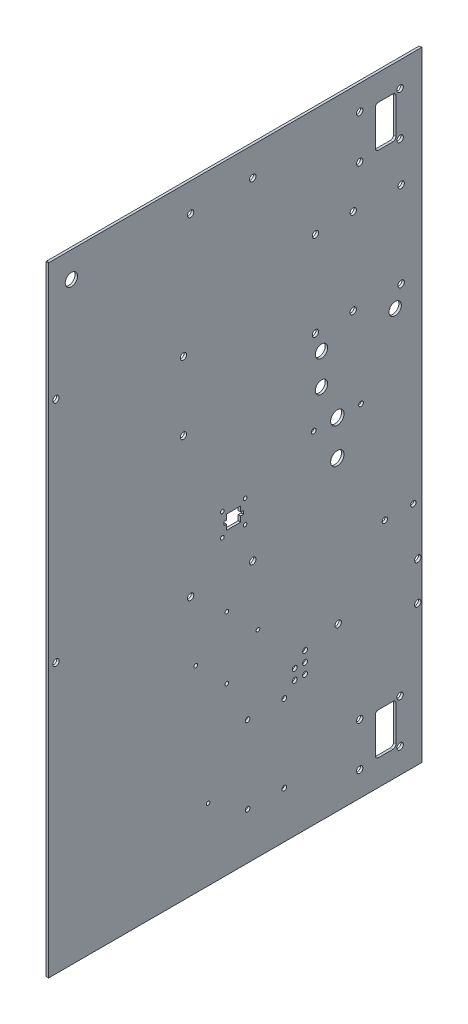
SolidWorks part; units mm, degrees
material "Acrylic (Medium-high impact)"
ref_plane "Front Plane" through (0, 0, 0) normal (0, 0, 1) x (1, 0, 0)
ref_plane "Top Plane" through (0, 0, 0) normal (0, 1, 0) x (1, 0, 0)
ref_plane "Right Plane" through (0, 0, 0) normal (1, 0, 0) x (0, 0, -1)
sketch "Sketch1" plane through (0, 0, 0) normal (1, 0, 0) x (0, 0, -1)
  line L0 (-249.6566, 398.5133) -> (-249.6566, 401.5867) construction
  line L1 (249.6566, -398.5133) -> (-249.6566, -398.5133)
  line L2 (249.6566, -398.5133) -> (249.6566, 398.5133)
  line L3 (249.6566, 398.5133) -> (-249.6566, 398.5133)
  line L4 (-249.6566, -398.5133) -> (-249.6566, 398.5133)
  line L5 (249.6566, -398.5133) -> (-249.6566, 398.5133) construction
  line L6 (249.6566, 398.5133) -> (-249.6566, -398.5133) construction
  line L7 (-249.6566, -398.5133) -> (-249.6566, -411.2133) construction
  line L8 (-249.6566, 398.5133) -> (-252.73, 398.5133) construction
  point P0 (0, 0)
  dimension "D2" = 3.0734
  dimension "D3" = 12.7
  dimension "D4" = 812.8
  dimension "D5" = 3.0734
  dimension "D1" = 502.3866
extrude "SidePanel" add sketch "Sketch1" along normal blind 3.0734
sketch "Sketch2" plane through (3.0734, 0, 0) normal (1, 0, 0) x (0, 0, -1)
  line L0 (192.5066, 398.5133) -> (192.5066, 379.4633) construction
  line L1 (249.6566, 398.5133) -> (-249.6566, 398.5133) construction
  line L2 (249.6566, -398.5133) -> (249.6566, 398.5133) construction
  line L3 (192.5066, -398.5133) -> (192.5066, -379.4633) construction
  line L4 (-249.6566, -398.5133) -> (249.6566, -398.5133) construction
  line L7 (249.6566, 338.1883) -> (230.6066, 338.1883) construction
  circle A0 centre (192.5066, 388.9883) radius 2.8956
  circle A1 centre (192.5066, -388.9883) radius 2.8956
  dimension "D3" = 5.7912
  dimension "D1" = 19.05
  dimension "D4" = 19.05
  dimension "D6" = 19.05
  dimension "D2" = 38.1
extrude "TopBottomHoleMaster" cut sketch "Sketch2" against normal through all
pattern_linear "LPattern1" count 4 spacing 127.0677 along (0, 0, 1) of "TopBottomHoleMaster"
sketch "Sketch3" plane through (3.0734, 0, 0) normal (1, 0, 0) x (0, 0, -1)
  line L1 (249.6566, -398.5133) -> (249.6566, 398.5133) construction
  line L2 (249.6566, 315.8617) -> (230.6066, 315.8617) construction
  line L3 (249.6566, 398.5133) -> (249.6566, 401.5867) construction
  line L4 (249.6566, 398.5133) -> (-249.6566, 398.5133) construction
  line L8 (-245.8466, 315.8617) -> (-226.7966, 315.8617) construction
  line L10 (249.6566, -398.5133) -> (249.6566, 398.5133) construction
  circle A0 centre (-236.3216, 315.8617) radius 2.8956
  circle A1 centre (240.1316, 315.8617) radius 2.8956
  dimension "D5" = 5.7912
  dimension "D2" = 19.05
  dimension "D3" = 3.0734
  dimension "D4" = 85.725
  dimension "D1" = 457.4032
extrude "RearHolesMaster" cut sketch "Sketch3" against normal through all
pattern_linear "LPattern2" count 4 spacing 211.7344 along (0, -1, 0) of "RearHolesMaster"
sketch "Sketch4" plane through (0, 0, 0) normal (-1, 0, 0) x (0, 0, 1)
  line L0 (-249.6566, -398.5133) -> (-249.6566, 398.5133) construction
  line L1 (-249.6566, 398.5133) -> (-230.6066, 398.5133)
  line L2 (-249.6566, 398.5133) -> (-249.6566, 379.4633)
  line L3 (-249.6566, 379.4633) -> (-230.6066, 379.4633)
  line L4 (-230.6066, 398.5133) -> (-230.6066, 379.4633)
  line L5 (249.6566, 398.5133) -> (226.7966, 398.5133)
  line L6 (249.6566, 398.5133) -> (249.6566, 379.4633)
  line L7 (249.6566, 379.4633) -> (226.7966, 379.4633)
  line L8 (226.7966, 398.5133) -> (226.7966, 379.4633)
  line L9 (-249.6566, -398.5133) -> (-230.6066, -398.5133)
  line L10 (-249.6566, -398.5133) -> (-249.6566, -379.4633)
  line L11 (-249.6566, -379.4633) -> (-230.6066, -379.4633)
  line L12 (-230.6066, -398.5133) -> (-230.6066, -379.4633)
  line L13 (249.6566, -398.5133) -> (-249.6566, -398.5133) construction
  line L14 (236.3216, 315.8617) -> (236.3216, 379.4633) construction
  dimension "D1" = 19.05
  dimension "D2" = 9.525
extrude "CornerCuts" cut sketch "Sketch4" against normal through all
hole_wizard "#8 Clearance Hole4 Brain Mount" positions "Sketch13" profile "Sketch14" hole size "5/16" standard "ANSI Inch" end condition through all
sketch "Sketch13" plane through (0, 0, 0) normal (-1, 0, 0) x (0, 0, 1)
  line L1 (-23.3934, 344.4367) -> (52.8066, 344.4367) construction
  line L2 (-23.3934, 344.4367) -> (-23.3934, -61.9633) construction
  line L3 (-23.3934, -61.9633) -> (52.8066, -61.9633) construction
  line L4 (52.8066, 344.4367) -> (52.8066, -61.9633) construction
  line L6 (249.6566, 379.4633) -> (249.6566, -398.5133) construction
  line L7 (-230.6066, 398.5133) -> (226.7966, 398.5133) construction
  point P0 (-23.3934, 344.4367)
  point P2 (52.8066, 344.4367)
  point P4 (52.8066, -61.9633)
  point P6 (-23.3934, -61.9633)
  point P78 (-146.4564, 141.8717)
  point P80 (-146.4564, 247.2817)
  point P81 (61.5696, 197.4926)
  point P83 (61.5696, 113.4186)
  dimension "D3" = 196.85
  dimension "D4" = 54.0766
  dimension "D1" = 76.2
  dimension "D2" = 406.4
  dimension "D5" = 123.063
  dimension "D6" = 203.835
  dimension "D7" = 105.41
  dimension "D8" = 84.074
  dimension "D9" = 8.763
  dimension "D10" = 175.3819
sketch "Sketch14" plane through (0, 344.4367, -23.3934) normal (0, 1, 0) x (0, 0, 1)
  line L0 (0, 0) -> (0, 3.0734)
  line L1 (0, 3.0734) -> (3.9116, 3.0734)
  line L2 (3.9116, 3.0734) -> (3.9116, 0)
  line L5 (3.9116, 0) -> (0, 0)
  line L11 (0, -6.35) -> (0, 107.95) construction
  dimension "Thru Hole Dia." = 7.8232
  dimension "Thru Hole Depth" = 3.0734
hole_wizard "#8 Clearance Hole3 Pump Mounts" positions "Sketch15" profile "Sketch16" hole size "#8" standard "ANSI Inch" end condition through all
sketch "Sketch15" plane through (0, 0, 0) normal (-1, 0, 0) x (0, 0, 1)
  line L4 (8.3566, -100.0633) -> (8.3566, -176.2633) construction
  line L5 (8.3566, -100.0633) -> (8.3566, -61.9633) construction
  line L7 (8.3566, -138.1633) -> (46.4566, -138.1633) construction
  line L9 (8.3566, -138.1633) -> (-29.7434, -138.1633) construction
  line L10 (-23.3934, -61.9633) -> (52.8066, -61.9633) construction
  point P0 (46.4566, -138.1633)
  point P2 (8.3566, -100.0633)
  point P4 (8.3566, -176.2633)
  point P6 (-29.7434, -138.1633)
  dimension "D1" = 76.2
  dimension "D2" = 76.2
  dimension "D3" = 38.1
  dimension "D4" = 44.45
sketch "Sketch16" plane through (0, -138.1633, 46.4566) normal (0, 1, 0) x (0, 0, 1)
  line L0 (0, 0) -> (0, 3.0734)
  line L1 (0, 3.0734) -> (2.2479, 3.0734)
  line L2 (2.2479, 3.0734) -> (2.2479, 0)
  line L5 (2.2479, 0) -> (0, 0)
  line L11 (0, -6.35) -> (0, 107.95) construction
  dimension "Thru Hole Dia." = 4.4958
  dimension "Thru Hole Depth" = 3.0734
sketch "Sketch17" plane through (0, 0, 0) normal (-1, 0, 0) x (0, 0, 1)
  line L3 (-230.6066, 379.4633) -> (226.7966, 379.4633) construction
  line L4 (-230.6066, 379.4633) -> (-230.6066, -379.4633) construction
  line L5 (-230.6066, -379.4633) -> (249.6566, -379.4633) construction
  line L6 (-198.8566, 347.7133) -> (-173.4566, 347.7133)
  line L7 (-198.8566, 347.7133) -> (-198.8566, 296.9133)
  line L8 (-198.8566, 296.9133) -> (-173.4566, 296.9133)
  line L9 (-173.4566, 347.7133) -> (-173.4566, 296.9133)
  line L10 (-173.4566, -347.7133) -> (-173.4566, -296.9133)
  line L11 (-173.4566, -347.7133) -> (-198.8566, -347.7133)
  line L12 (-198.8566, -347.7133) -> (-198.8566, -296.9133)
  line L13 (-173.4566, -296.9133) -> (-198.8566, -296.9133)
  line L14 (249.6566, 379.4633) -> (249.6566, -398.5133) construction
  dimension "D1" = 25.4
  dimension "D4" = 50.8
  dimension "D2" = 50.8
  dimension "D3" = 25.4
  dimension "D5" = 31.75
  dimension "D6" = 31.75
  dimension "D7" = 31.75
extrude "Cable Pass Through" cut sketch "Sketch17" against normal through all
hole_wizard "#8 Clearance Hole1 Pass through Mounting holes" positions "Sketch48" profile "Sketch49" hole size "5/16" standard "ANSI Inch" end condition through all
sketch "Sketch48" plane through (3.0734, 0, 0) normal (1, 0, 0) x (0, 0, -1)
  line L21 (154.4066, 348.9833) -> (154.4066, 295.6433) construction
  line L24 (203.9366, 348.9833) -> (203.9366, 295.6433) construction
  line L27 (203.9366, 322.3133) -> (154.4066, 322.3133) construction
  line L30 (173.4566, 322.3133) -> (198.8566, 322.3133) construction
  line L31 (173.4566, 296.9133) -> (173.4566, 347.7133) construction
  line L32 (198.8566, 347.7133) -> (198.8566, 296.9133) construction
  line L34 (173.4566, 296.9133) -> (173.4566, 347.7133) construction
  line L36 (154.4066, -295.6433) -> (154.4066, -348.9833) construction
  line L37 (154.4066, -322.3133) -> (173.4566, -322.3133) construction
  line L38 (173.4566, -347.7133) -> (173.4566, -296.9133) construction
  line L41 (203.9366, -295.6433) -> (203.9366, -348.9833) construction
  line L44 (198.8566, -322.3133) -> (203.9366, -322.3133) construction
  line L45 (198.8566, -296.9133) -> (198.8566, -347.7133) construction
  point P0 (154.4066, -348.9833)
  point P2 (203.9366, -348.9833)
  point P4 (203.9366, -295.6433)
  point P6 (154.4066, -295.6433)
  point P63 (154.4066, 348.9833)
  point P65 (203.9366, 348.9833)
  point P67 (203.9366, 295.6433)
  point P69 (154.4066, 295.6433)
  dimension "D1" = 5.08
  dimension "D2" = 19.05
  dimension "D3" = 53.34
  dimension "D4" = 5.08
  dimension "D5" = 19.05
  dimension "D6" = 53.34
sketch "Sketch49" plane through (3.0734, -348.9833, -154.4066) normal (0, 1, 0) x (0, 0, -1)
  line L0 (0, 0) -> (0, 3.0734)
  line L1 (0, 3.0734) -> (3.9116, 3.0734)
  line L2 (3.9116, 3.0734) -> (3.9116, 0)
  line L5 (3.9116, 0) -> (0, 0)
  line L11 (0, -6.35) -> (0, 107.95) construction
  dimension "Thru Hole Dia." = 7.8232
  dimension "Thru Hole Depth" = 3.0734
hole_wizard "#8 Clearance Hole3 Sensor Mounts" positions "Sketch25" profile "Sketch24" hole size "#8" standard "ANSI Inch"
sketch "Sketch25" plane through (0, 0, 0) normal (-1, 0, 0) x (0, 0, 1)
  line L3 (-21.0566, -36.5633) -> (55.1434, -36.5633) construction
  line L4 (-21.0566, -36.5633) -> (-21.0566, 39.6367) construction
  line L5 (-21.0566, 39.6367) -> (55.1434, 39.6367) construction
  line L6 (55.1434, -36.5633) -> (55.1434, 39.6367) construction
  line L8 (-21.0566, 39.6367) -> (55.1434, 39.6367) construction
  line L9 (-21.0566, 39.6367) -> (-21.0566, 77.7367) construction
  line L10 (-21.0566, 77.7367) -> (55.1434, 77.7367) construction
  line L11 (55.1434, 39.6367) -> (55.1434, 77.7367) construction
  point P38 (55.1434, 39.6367)
  point P135 (-21.0566, 39.6367)
  point P146 (55.1434, 77.7367)
  point P235 (-21.0566, 77.7367)
  dimension "D1" = 76.2
  dimension "D2" = 76.2
  dimension "D3" = 38.1
  dimension "D4" = 76.2
sketch "Sketch24" plane through (0, 39.6367, 55.1434) normal (0, 1, 0) x (0, 0, 1)
  line L0 (0, 0) -> (0, 3.0734)
  line L1 (0, 3.0734) -> (2.2479, 3.0734)
  line L2 (2.2479, 3.0734) -> (2.2479, 0)
  line L5 (2.2479, 0) -> (0, 0)
  line L11 (0, -6.35) -> (0, 107.95) construction
  dimension "Thru Hole Dia." = 4.4958
  dimension "Thru Hole Depth" = 3.0734
sketch "Sketch39" plane through (0, 0, 0) normal (-1, 0, 0) x (0, 0, 1)
  line L0 (-249.6566, 398.5133) -> (-249.6566, 418.9221) construction
  line L1 (-230.2256, 398.5133) -> (-230.6066, 398.5133)
  line L2 (-249.6566, -398.5133) -> (-249.6566, -414.8093) construction
  line L3 (-230.6066, 398.5133) -> (-230.6066, 379.4633)
  line L4 (-230.6066, 379.4633) -> (-249.6566, 379.4633)
  line L5 (-249.6566, 379.0823) -> (-230.2256, 379.0823)
  line L6 (-230.2256, 398.5133) -> (-230.2256, 379.0823)
  line L7 (-249.6566, -398.5133) -> (-270.6931, -398.5133) construction
  line L8 (-249.6566, -379.0823) -> (-249.6566, -379.4633)
  line L9 (-249.6566, -379.4633) -> (-230.6066, -379.4633)
  line L10 (-230.6066, -379.4633) -> (-230.6066, -398.5133)
  line L11 (-249.6566, -379.0823) -> (-230.2256, -379.0823)
  line L12 (-230.2256, -398.5133) -> (-230.2256, -379.0823)
  line L13 (-230.6066, -398.5133) -> (-230.2256, -398.5133)
  line L14 (-249.6566, 379.4633) -> (-249.6566, 379.0823)
  line L15 (226.7966, 398.5133) -> (226.4156, 398.5133)
  line L16 (-230.6066, 398.5133) -> (226.7966, 398.5133) construction
  line L17 (226.4156, 398.5133) -> (226.4156, 379.0823)
  line L18 (249.6566, 379.0823) -> (226.4156, 379.0823)
  line L19 (249.6566, 379.4633) -> (249.6566, -398.5133) construction
  line L20 (226.7966, 398.5133) -> (226.7966, 379.4633)
  line L21 (226.7966, 379.4633) -> (249.6566, 379.4633)
  line L22 (249.6566, 379.4633) -> (249.6566, 379.0823)
  dimension "D1" = 19.431
  dimension "D2" = 19.431
  dimension "D3" = 19.431
  dimension "D4" = 19.431
  dimension "D5" = 0.381
extrude "Cut-Extrude1" cut sketch "Sketch39" against normal blind 2.54
hole_wizard "#8 Clearance Hole -hx mount" positions "Sketch40" profile "Sketch41" hole size "5/16" standard "ANSI Inch" end condition through all
sketch "Sketch40" plane through (3.0734, 0, 0) normal (1, 0, 0) x (0, 0, -1)
  line L0 (230.6066, 398.5133) -> (-226.7966, 398.5133) construction
  line L1 (249.6566, -379.4633) -> (249.6566, 379.4633) construction
  point P0 (205.2066, 246.1133)
  point P2 (205.2066, 141.1133)
  point P4 (100.2066, 141.1133)
  point P6 (100.2066, 246.1133)
  dimension "D1" = 152.4
  dimension "D2" = 44.45
  dimension "D3" = 105
  dimension "D4" = 105
sketch "Sketch41" plane through (3.0734, 246.1133, -205.2066) normal (0, 1, 0) x (0, 0, -1)
  line L0 (0, 0) -> (0, 3.0734)
  line L1 (0, 3.0734) -> (3.9116, 3.0734)
  line L2 (3.9116, 3.0734) -> (3.9116, 0)
  line L5 (3.9116, 0) -> (0, 0)
  line L11 (0, -6.35) -> (0, 107.95) construction
  dimension "Thru Hole Dia." = 7.8232
  dimension "Thru Hole Depth" = 3.0734
sketch "Sketch42" plane through (3.0734, 0, 0) normal (1, 0, 0) x (0, 0, -1)
  line L0 (100.2066, 141.1133) -> (205.2066, 141.1133) construction
  line L1 (107.5726, 118.5073) -> (197.8406, 118.5073) construction
  line L2 (152.7066, 141.1133) -> (152.7066, 118.5073) construction
  circle A0 centre (197.8406, 118.5073) radius 7.5787
  circle A1 centre (107.5726, 118.5073) radius 7.5819
  circle A2 centre (197.8406, 118.5073) radius 21.6881 construction
  dimension "D1" = 15.1574
  dimension "D2" = 15.1638
  dimension "D4" = 22.606
  dimension "D3" = 7.366
extrude "Coolant hose pass through" cut sketch "Sketch42" against normal through all
sketch "Sketch43" plane through (3.0734, 0, 0) normal (1, 0, 0) x (0, 0, -1)
  line L0 (-249.6566, 379.4633) -> (-249.6566, -398.5133) construction
  line L1 (230.6066, 398.5133) -> (-226.7966, 398.5133) construction
  line L2 (107.5726, 118.5073) -> (197.8406, 118.5073) construction
  line L3 (107.5726, 118.5073) -> (107.5726, 80.4073) construction
  circle A0 centre (-198.8566, 347.7133) radius 7.5819
  circle A1 centre (107.5726, 80.4073) radius 7.5819
  dimension "D1" = 15.1638
  dimension "D4" = 15.1638
  dimension "D5" = 38.1
  dimension "D2" = 50.8
  dimension "D3" = 50.8
extrude "Air flush in/out" cut sketch "Sketch43" against normal through all
hole_wizard "#8 Clearance Hole2 Air Flush Out mount" positions "Sketch44" profile "Sketch45" hole size "5/16" standard "ANSI Inch" end condition through all
sketch "Sketch44" plane through (3.0734, 0, 0) normal (1, 0, 0) x (0, 0, -1)
  line L0 (249.6566, -379.4633) -> (249.6566, 379.4633) construction
  line L1 (-249.6566, -398.5133) -> (230.6066, -398.5133) construction
  point P0 (225.5266, -160.7693)
  point P2 (225.5266, -208.0133)
  point P4 (128.0678, -181.1548)
  dimension "D1" = 47.244
  dimension "D2" = 99.568
  dimension "D3" = 101.092
  dimension "D4" = 24.13
  dimension "D5" = 190.5
sketch "Sketch45" plane through (3.0734, -160.7693, -225.5266) normal (0, 1, 0) x (0, 0, -1)
  line L0 (0, 0) -> (0, 3.0734)
  line L1 (0, 3.0734) -> (3.9116, 3.0734)
  line L2 (3.9116, 3.0734) -> (3.9116, 0)
  line L5 (3.9116, 0) -> (0, 0)
  line L11 (0, -6.35) -> (0, 107.95) construction
  dimension "Thru Hole Dia." = 7.8232
  dimension "Thru Hole Depth" = 3.0734
hole_wizard "#8 Clearance Hole4 Panel Mounts" positions "Sketch46" profile "Sketch47" hole size "5/16" standard "ANSI Inch" end condition through all
sketch "Sketch46" plane through (3.0734, 0, 0) normal (1, 0, 0) x (0, 0, -1)
  line L0 (-249.6566, 379.4633) -> (-249.6566, -398.5133) construction
  line L1 (230.6066, 398.5133) -> (-226.7966, 398.5133) construction
  point P0 (-217.7034, 230.1367)
  point P6 (-217.7034, -49.2633)
  dimension "D1" = 31.9532
  dimension "D2" = 168.3766
  dimension "D3" = 279.4
sketch "Sketch47" plane through (3.0734, 230.1367, 217.7034) normal (0, 1, 0) x (0, 0, -1)
  line L0 (0, 0) -> (0, 3.0734)
  line L1 (0, 3.0734) -> (3.9116, 3.0734)
  line L2 (3.9116, 3.0734) -> (3.9116, 0)
  line L5 (3.9116, 0) -> (0, 0)
  line L11 (0, -6.35) -> (0, 107.95) construction
  dimension "Thru Hole Dia." = 7.8232
  dimension "Thru Hole Depth" = 3.0734
fillet "Fillet1" radius 3.81 8 edges at (1.5367, -296.9133, -173.4566) (1.5367, -296.9133, -198.8566) (1.5367, -347.7133, -198.8566) (1.5367, -347.7133, -173.4566) (1.5367, 347.7133, -198.8566) (1.5367, 347.7133, -173.4566) (1.5367, 296.9133, -198.8566) (1.5367, 296.9133, -173.4566)
sketch "Sketch50" plane through (3.0734, 0, 0) normal (1, 0, 0) x (0, 0, -1)
  line L0 (-8.625, 3.8117) -> (8.625, 3.8117)
  line L1 (8.625, 3.8117) -> (8.625, -2.6883)
  line L2 (8.625, -2.6883) -> (12.125, -2.6883)
  line L3 (12.125, -2.6883) -> (12.125, -6.9383)
  line L4 (12.125, -6.9383) -> (8.625, -6.9383)
  line L5 (8.625, -6.9383) -> (8.625, -13.4383)
  line L6 (8.625, -13.4383) -> (-8.625, -13.4383)
  line L7 (-8.625, -13.4383) -> (-8.625, -6.9383)
  line L8 (-8.625, -6.9383) -> (-12.125, -6.9383)
  line L9 (-12.125, -6.9383) -> (-12.125, -2.6883)
  line L10 (-12.125, -2.6883) -> (-8.625, -2.6883)
  line L11 (-8.625, -2.6883) -> (-8.625, 3.8117)
  line L12 (127, -4.8133) -> (127, 38.3667) construction
  line L17 (0, 3.8117) -> (0, -13.4383) construction
  line L18 (-12.125, -4.8133) -> (12.125, -4.8133) construction
  line L19 (-3.4982, 3.8117) -> (-3.4982, -13.4383) construction
  line L20 (127, -4.8133) -> (0, -4.8133) construction
  line L21 (13.97, 9.1567) -> (13.97, -18.7833) construction
  line L22 (-249.6566, -9.525) -> (249.6566, -9.525) construction
  line L23 (98, 38.3667) -> (156, 38.3667) construction
  line L24 (-19.05, 14.2367) -> (19.05, 14.2367) construction
  line L25 (19.05, 14.2367) -> (19.05, -23.8633) construction
  line L26 (-13.97, -18.7833) -> (13.97, -18.7833) construction
  line L27 (-19.05, -23.8633) -> (-19.05, 14.2367) construction
  line L28 (-19.05, -4.8133) -> (19.05, -4.8133) construction
  line L29 (0, 14.2367) -> (0, -23.8633) construction
  line L30 (0, -13.4383) -> (0, -18.7833) construction
  line L31 (-249.6566, -398.5133) -> (230.6066, -398.5133) construction
  line L32 (0, 398.5133) -> (0, -398.5133) construction
  line L41 (230.6066, -379.4633) -> (249.6566, -379.4633)
  line L42 (249.6566, -379.4633) -> (249.6566, 379.4633)
  line L43 (249.6566, 379.4633) -> (230.6066, 379.4633)
  line L44 (230.6066, 379.4633) -> (230.6066, 398.5133)
  line L45 (230.6066, 398.5133) -> (-226.7966, 398.5133)
  line L46 (-226.7966, 398.5133) -> (-226.7966, 379.4633)
  line L47 (-226.7966, 379.4633) -> (-249.6566, 379.4633)
  line L48 (-249.6566, 379.4633) -> (-249.6566, -398.5133)
  line L49 (-249.6566, -398.5133) -> (230.6066, -398.5133)
  line L50 (230.6066, -398.5133) -> (230.6066, -379.4633)
  line L51 (230.6066, -379.4633) -> (249.6566, -379.4633)
  line L52 (249.6566, -379.4633) -> (249.6566, 379.4633)
  line L53 (249.6566, 379.4633) -> (230.6066, 379.4633)
  line L54 (230.6066, 379.4633) -> (230.6066, 398.5133)
  line L55 (230.6066, 398.5133) -> (-226.7966, 398.5133)
  line L56 (-226.7966, 398.5133) -> (-226.7966, 379.4633)
  line L57 (-226.7966, 379.4633) -> (-249.6566, 379.4633)
  line L58 (-249.6566, 379.4633) -> (-249.6566, -398.5133)
  line L59 (-249.6566, -398.5133) -> (230.6066, -398.5133)
  line L60 (230.6066, -398.5133) -> (230.6066, -379.4633)
  circle A0 centre (127, -4.8133) radius 8.1915
  circle A1 centre (127, 38.3667) radius 8.1915
  point P17 (0, 3.8117)
  point P26 (0, -4.8133)
  point P27 (-3.4982, -4.8133)
  point P28 (-13.97, -18.7833)
  point P31 (13.97, -18.7833)
  point P34 (98, 38.3667)
  point P35 (156, 38.3667)
  point P38 (127, 38.3667)
  point P47 (0, -4.8133)
  point P48 (-13.97, 9.1567)
  point P49 (13.97, 9.1567)
  point P52 (13.97, -4.8133)
  point P67 (0, -9.525)
  dimension "D2" = 16.383
  dimension "D19" = 16.383
  dimension "D3" = 17.25
  dimension "D4" = 17.25
  dimension "D7" = 4.25
  dimension "D8" = 24.25
  dimension "D9" = 127
  dimension "D10" = 393.7
  dimension "D12" = 43.18
  dimension "D13" = 58
  dimension "D14" = 38.1
  dimension "D15" = 38.1
  dimension "D16" = 27.94
  dimension "D17" = 27.94
  dimension "D18" = 0
extrude "Sensor Mounting" cut sketch "Sketch50" against normal through all flip side to cut
hole_wizard "#8 Clearance Hole1" positions "Sketch51" profile "Sketch52" hole size "#8" standard "ANSI Inch" end condition through all
sketch "Sketch51" plane through (3.0734, 0, 0) normal (1, 0, 0) x (0, 0, -1)
  point P0 (-13.97, 9.1567)
  point P3 (13.97, 9.1567)
  point P6 (13.97, -18.7833)
  point P9 (-13.97, -18.7833)
sketch "Sketch52" plane through (3.0734, 9.1567, 13.97) normal (0, 1, 0) x (0, 0, -1)
  line L0 (0, 0) -> (0, 3.0734)
  line L1 (0, 3.0734) -> (2.2479, 3.0734)
  line L2 (2.2479, 3.0734) -> (2.2479, 0)
  line L5 (2.2479, 0) -> (0, 0)
  line L11 (0, -6.35) -> (0, 107.95) construction
  dimension "Thru Hole Dia." = 4.4958
  dimension "Thru Hole Depth" = 3.0734
hole_wizard "#12 Clearance Hole1" positions "Sketch53" profile "Sketch54" hole size "#12" standard "ANSI Inch" end condition through all
sketch "Sketch53" plane through (3.0734, 0, 0) normal (1, 0, 0) x (0, 0, -1)
  point P0 (98, 38.3667)
  point P3 (156, 38.3667)
sketch "Sketch54" plane through (3.0734, 38.3667, -98) normal (0, 1, 0) x (0, 0, -1)
  line L0 (0, 0) -> (0, 3.0734)
  line L1 (0, 3.0734) -> (2.8956, 3.0734)
  line L2 (2.8956, 3.0734) -> (2.8956, 0)
  line L5 (2.8956, 0) -> (0, 0)
  line L11 (0, -6.35) -> (0, 107.95) construction
  dimension "Thru Hole Dia." = 5.7912
  dimension "Thru Hole Depth" = 3.0734
fillet "Fillet2" radius 0.127 12 edges at (1.5367, -13.4383, 8.625) (1.5367, -6.9383, -12.125) (1.5367, -13.4383, -8.625) (1.5367, -6.9383, -8.625) (1.5367, -2.6883, -12.125) (1.5367, -2.6883, -8.625) (1.5367, -6.9383, 8.625) (1.5367, -2.6883, 8.625) (1.5367, -2.6883, 12.125) (1.5367, -6.9383, 12.125) (1.5367, 3.8117, -8.625) (1.5367, 3.8117, 8.625)
hole_wizard "#4 Clearance Hole compressor driver" positions "Sketch55" profile "Sketch56" hole size "#12" standard "ANSI Inch" end condition through all
sketch "Sketch55" plane through (0, 0, 0) normal (-1, 0, 0) x (0, 0, 1)
  line L0 (249.6566, -398.5133) -> (-230.2256, -398.5133) construction
  line L2 (249.6566, 379.0823) -> (249.6566, -398.5133) construction
  point P0 (-17.0434, -227.3133)
  point P2 (-62.0434, -227.3133)
  point P4 (-62.0434, -322.3133)
  point P6 (-17.0434, -322.3133)
  dimension "D1" = 45
  dimension "D2" = 95
  dimension "D3" = 76.2
  dimension "D4" = 266.7
sketch "Sketch56" plane through (0, -227.3133, -17.0434) normal (0, 1, 0) x (0, 0, 1)
  line L0 (0, 0) -> (0, 3.0734)
  line L1 (0, 3.0734) -> (2.8956, 3.0734)
  line L2 (2.8956, 3.0734) -> (2.8956, 0)
  line L5 (2.8956, 0) -> (0, 0)
  line L11 (0, -6.35) -> (0, 107.95) construction
  dimension "Thru Hole Dia." = 5.7912
  dimension "Thru Hole Depth" = 3.0734
hole_wizard "1/4 Clearance Hole ball valve u bolt" positions "Sketch57" profile "Sketch58" hole size "1/4" standard "ANSI Inch" end condition through all
sketch "Sketch57" plane through (3.0734, 0, 0) normal (1, 0, 0) x (0, 0, -1)
  line L0 (-249.6566, -398.5133) -> (230.6066, -398.5133) construction
  line L1 (249.6566, -379.4633) -> (249.6566, 379.4633) construction
  point P0 (220.1418, -99.7331)
  point P2 (185.2168, -99.7331)
  dimension "D1" = 298.7802
  dimension "D2" = 29.5148
  dimension "D3" = 34.925
sketch "Sketch58" plane through (3.0734, -99.7331, -220.1418) normal (0, 1, 0) x (0, 0, -1)
  line L0 (0, 0) -> (0, 3.0734)
  line L1 (0, 3.0734) -> (3.2639, 3.0734)
  line L2 (3.2639, 3.0734) -> (3.2639, 0)
  line L5 (3.2639, 0) -> (0, 0)
  line L11 (0, -6.35) -> (0, 107.95) construction
  dimension "Thru Hole Dia." = 6.5278
  dimension "Thru Hole Depth" = 3.0734
hole_wizard "Aeration Pump #8 Clearance Hole1" positions "Sketch59" profile "Sketch60" hole size "#8" standard "ANSI Inch" end condition through all
sketch "Sketch59" plane through (3.0734, 0, 0) normal (1, 0, 0) x (0, 0, -1)
  line L0 (-36.1378, -296.9133) -> (-5.1816, -296.9133) construction
  line L1 (-5.1816, -296.9133) -> (-5.1816, -286.5946) construction
  line L2 (-5.1816, -286.5946) -> (-36.1378, -286.5946) construction
  line L3 (-36.1378, -286.5946) -> (-36.1378, -296.9133) construction
  line L6 (-36.1378, -291.7539) -> (-5.1816, -291.7539) construction
  line L9 (-31.3753, -286.5946) -> (-31.3753, -296.9133) construction
  circle A0 centre (17.0434, -322.3133) radius 2.8956 construction
  point P0 (-31.3753, -291.7539)
  dimension "D4" = 22.225
  dimension "D5" = 25.4
  dimension "D1" = 10.3187
  dimension "D2" = 30.9562
  dimension "D3" = 4.7625
sketch "Sketch60" plane through (3.0734, -291.7539, 31.3753) normal (0, 1, 0) x (0, 0, -1)
  line L0 (0, 0) -> (0, 3.0734)
  line L1 (0, 3.0734) -> (2.1526, 3.0734)
  line L2 (2.1526, 3.0734) -> (2.1527, 0)
  line L5 (2.1527, 0) -> (0, 0)
  line L11 (0, -6.35) -> (0, 107.95) construction
  dimension "Thru Hole Dia." = 4.3053
  dimension "Thru Hole Depth" = 3.0734
sketch "Nutrient Holes" plane through (3.0734, 0, 0) normal (1, 0, 0) x (0, 0, -1)
  line L0 (-249.6566, -398.5133) -> (230.6066, -398.5133) construction
  circle A0 centre (87.4434, -214.3633) radius 3.0226
  circle A1 centre (62.0434, -227.3133) radius 2.8956 construction
  dimension "D1" = 6.0452
  dimension "D2" = 184.15
  dimension "D3" = 25.4
extrude "Nutrient Hoses" cut sketch "Nutrient Holes" against normal through all
pattern_linear "LPattern3" count 3 spacing 12.7 along (0, 1, 0) count 3 spacing 12.7 along (0, 0, 1) skipping (0, 2), (1, 2), (2, 1), (2, 2) of "Nutrient Hoses"
sketch "Sketch61" plane through (3.0734, 0, 0) normal (1, 0, 0) x (0, 0, -1)
  line L0 (-226.7966, 379.4633) -> (230.6066, 379.4633)
  line L1 (230.6066, 379.4633) -> (230.6066, -379.4633)
  line L2 (-226.7966, 379.4633) -> (-226.7966, -379.4633)
  line L3 (-226.7966, -379.4633) -> (230.6066, -379.4633)
  line L4 (-252.1966, 404.8633) -> (-252.1966, -404.8633)
  line L5 (-252.1966, -404.8633) -> (256.0066, -404.8633)
  line L6 (256.0066, 404.8633) -> (256.0066, -404.8633)
  line L7 (-252.1966, 404.8633) -> (256.0066, 404.8633)
  dimension "D1" = 25.4
extrude "Cut-Extrude2" cut sketch "Sketch61" against normal through all
equation "\"Height\"= 32in"
equation "\"Width\"= 23in"
equation "\"Depth\"= 20in"
equation "\"Plexi\"= .121in"
equation "\"Cutwidth\"= .016in"
equation "\"Earsize\"= 1in + \"Cutwidth\" /2"
equation "\"Slotsize\" = 1in - \"CutWidth\" / 2"
equation "\"InnerWidth\" = \"Width\" - 2* \"Plexi\""
equation "\"InnerHeight\" = \"Height\" -2 * \"Plexi\""
equation "\"InnerDepth\" = \"Depth\" - 2*\"Plexi\""
equation "\"RearHoleSpacing\" = (\"Width\" - 2*\"RearHolesBorder\") / (\"RearNumHoles\"-1)"
equation "\"RivetDia\" = .228in"
equation "\"SlotDepth\" = \"Plexi\" + 0.75in + .005in"
equation "\"SideSlotWidth\"   = \"Plexi\"+.005in"
equation "\"SidePanelVertSpacing\" = (\"Height\"-2*(1.75-\"Plexi\")) / 5"
equation "\"BottomPanelSideHoleSpacing\" = (\"InnerDepth\"-2*(1.75-\"Plexi\")) / 4"
equation "\"D1@Sketch1\"=\"TopDepth\""
equation "\"D2@Sketch1\"=\"Plexi\""
equation "\"D1@SidePanel\"=\"Plexi\""
equation "\"MagnetThickness\"= 0.125in"
equation "\"MagnetDiameter\"= 12mm"
equation "\"DoorPlexi\" = \"Plexi\""
equation "\"Boxsize\" = .75in"
equation "\"Boxinner\" = .625in"
equation "\"CornerCube\" = 0.75in"
equation "\"FingerLength\" = 1.125in"
equation "\"RearNumHoles\" = 4"
equation "\"RearHolesBorder\" = 2.25"
equation "\"RearBarLength\" = (\"InnerWidth\"-2*\"CornerCube\")"
equation "\"RearTopNumHoles\" = 4"
equation "\"RearTopHolesBorder\" = 3.1"
equation "\"RearTopHolesSpacing\" = (\"Width\" - 2*\"RearTopHolesBorder\") / (\"RearTopNumHoles\"-1)"
equation "\"SideTopNumHoles\" = 4"
equation "\"SideTopHoleOffset\"=\"CornerCube\"+\"FingerLength\"+\"Plexi\"+.5"
equation "\"SideTopHoleSpacing\" = (\"TopBarDepth\"-2*\"SideTopHoleOffset\") / (\"SideTopNumHoles\"-1)"
equation "\"SideHorizNumHoles\" = 4"
equation "\"SideHorizHoleBorder\" = 1.50"
equation "\"SideHorizHoleSpacing\" = (\"TopBarDepth\"-2*\"SideHorizHoleBorder\") / (\"SideHorizNumHoles\"-1)"
equation "\"SideVertNumHoles\" = 4"
equation "\"SideVertHolesBorder\" = \"CornerCube\"+\"FingerLength\"+1.50"
equation "\"SideVertHoleSpacing\" = (\"InnerHeight\" - 2*\"SideVertHolesBorder\") / (\"SideVertNumHoles\"-1)"
equation "\"FrontDoorGap\" = .1in"
equation "\"TopDepth\" = \"Depth\"-\"DoorPlexi\"-\"FrontDoorGap\""
equation "\"TopBarDepth\" = \"Depth\"-\"DoorPlexi\"-\"Plexi\"-2*\"MagnetThickness\"-2*\"CornerCube\""
equation "\"D1@Sketch2\"=\"Boxsize\""
equation "\"D2@Sketch2\"=\"SideHorizHoleBorder\""
equation "\"D3@Sketch2\"=\"RivetDia\""
equation "\"D4@Sketch2\"=\"Boxsize\""
equation "\"D3@LPattern1\"=\"SideHorizHoleSpacing\""
equation "\"D1@LPattern1\"=\"SideHorizNumHoles\""
equation "\"D2@Sketch3\"=\"Boxsize\""
equation "\"D3@Sketch3\"=\"Plexi\""
equation "\"D4@Sketch3\"=\"SideVertHolesBorder\""
equation "\"D5@Sketch3\"=\"RivetDia\""
equation "\"D3@LPattern2\"=\"SideVertHoleSpacing\""
equation "\"D1@LPattern2\"=\"SideVertNumHoles\""
equation "\"BasePlateThickness\" = 0.5in"
equation "\"SideVertBarLength\"=\"Height\"-\"BasePlateThickness\"-2*\"CornerCube\"-\"Plexi\""
equation "\"RearSideVertNumHoles\" = 4"
equation "\"RearSideVertHolesBorder\" = 2.4"
equation "\"RearSideVertHoleSpacing\" = (\"InnerHeight\" - 2*\"RearSideVertHolesBorder\") / (\"RearSideVertNumHoles\"-1)"
equation "\"D3@Sketch1\"=\"BasePlateThickness\""
equation "\"D4@Sketch1\"=\"Height\""
equation "\"D6@Sketch2\"=\"CornerCube\""
equation "\"D1@Sketch4\"=\"Boxsize\""
equation "\"D5@Sketch1\"=\"Plexi\""
equation "\"BasePlateWidth\" = \"Width\"+\"EBWidth\"-2*\"Plexi\""
equation "\"BasePlateDepth\" = \"TopBarDepth\"+2*\"CornerCube\""
equation "\"FingerWidth\" = .625in"
equation "\"CoolerDepth\" = 12in"
equation "\"ShelfDepth\" = \"TopBarDepth\"+\"CornerCube\"-\"CoolerDepth\""
equation "\"IntakeWidth\"=4in"
equation "\"IntakeHeight\"=2in"
equation "\"ExhaustWidth\"=4in"
equation "\"ExhaustHeight\"=2in"
equation "\"VentSpacing\"=7in"
equation "\"D1@Sketch3\"=\"TopBarDepth\""
equation "\"BoxsizeHalf\" = \"Boxsize\"/2"
equation "\"D2@Sketch4\"=\"BoxsizeHalf\""
equation "\"EBWidth\" = 9in"
equation "\"ShelfGap\" = 0.5in"
equation "\"ShelfBarDepth\"=\"ShelfDepth\"-2*\"CornerCube\""
equation "\"ShelfWidth\" = \"EBWidth\"-\"ShelfGap\""
equation "\"ShelfBarWidth\" = \"EBWidth\"-\"Boxsize\""
equation "\"ShelfBarWidthShort\" = \"ShelfBarWidth\"-\"Boxsize\"-\"ShelfGap\""
equation "\"VentVertLocation\"=12.75in"
equation "\"AngleBracketLength\"=20mm"
equation "\"AngleBracketWidth\"=.5in"
equation "\"AngleBracketThickness\"=.125in"
equation "\"AngleBracketHolePos\"=15mm"
equation "\"AngleBracketHoleDia\"=\"Rivet3_16Dia\""
equation "\"ShelfBarAngleHole\"=\"ShelfGap\"+\"Boxsize\"+\"AngleBracketHolePosShort\""
equation "\"ComponentMountDia\"=0.1770"
equation "\"ShelfThickness\" = .1250in"
equation "\"Rivet3_16Dia\" = .191in"
equation "\"BinderPostDia\" = .228in"
equation "\"ShelfHeight1\" = 13in"
equation "\"ShelfHeight2\" = 24in"
equation "\"AngleBracketLengthShort\"=.625in"
equation "\"AngleBracketLengthLong\"=1in"
equation "\"AngleBracketHolePosShort\"=.358in"
equation "\"AngleBracketHolePosLong\"=.7in"
equation "\"PSBracketThickness\" = .0641in"
equation "\"EBForwardMountOffset\" = 4.0in"
equation "\"EBForwardMount\" = 2*\"Boxsize\"+\"CoolerDepth\"+\"EBForwardMountOffset\""
equation "\"EBRearwardMountOffset\" = 1.5in"
equation "\"EBRearwardMount\"= \"Boxsize\"+\"EBRearwardMountOffset\""
equation "\"MagSealWidth\" = \"InnerWidth\""
equation "\"MagSealHeight\" = \"Height\"-\"BasePlateThickness\"-\"Plexi\""
equation "\"MagWidth\" = .500in"
equation "\"SiliconeSealOD\" = .3125in"
equation "\"SiliconeSealID\" = .1875in"
equation "\"SiliconeSealWidth\" = \"MagSealWidth\" - 2*\"MagWidth\"-\"SiliconeSealOD\""
equation "\"SiliconeSealHeigth\" = \"MagSealHeight\" - 2*\"MagWidth\"-\"SiliconeSealOD\""
equation "\"HooknLoopThick\" = .085in"
equation "\"HooknLoopWidth\" = 0.75in"
equation "\"HooknLoopHeigth\" = 0.75in"
equation "\"CoolantHosePassThrough\"=0.59675"
equation "\"D1@Sketch42\"=\"CoolantHosePassThrough\""
equation "\"HumiditySensorClearanceHole\"=0.65625"
